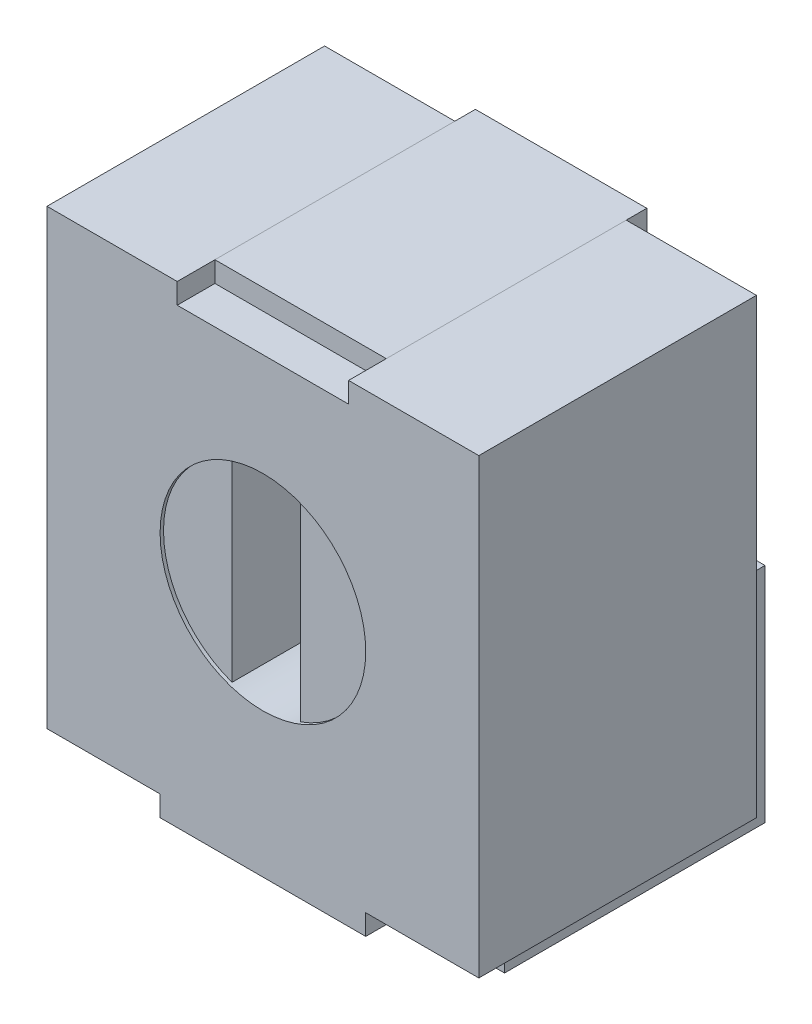
SolidWorks part; units mm, degrees
ref_plane "Front Plane" through (0, 0, 0) normal (0, 0, 1) x (1, 0, 0)
ref_plane "Top Plane" through (0, 0, 0) normal (0, 1, 0) x (1, 0, 0)
ref_plane "Right Plane" through (0, 0, 0) normal (1, 0, 0) x (0, 0, -1)
sketch "Sketch1" plane through (0, 0, 0) normal (0, 0, 1) x (1, 0, 0)
  line L0 (1.6002, 3.2004) -> (1.6002, -0.1524) construction
  line L1 (0, 0) -> (0.8382, 0)
  line L2 (0, 0) -> (0, 3.3528)
  line L3 (0, 3.3528) -> (0.9652, 3.3528)
  line L4 (3.2004, 0) -> (3.2004, 3.3528)
  line L5 (2.3622, 0) -> (3.2004, 0)
  line L6 (2.2352, 3.3528) -> (3.2004, 3.3528)
  line L7 (0.8382, 0) -> (0.8382, -0.1524)
  line L8 (0.8382, -0.1524) -> (2.3622, -0.1524)
  line L9 (2.3622, 0) -> (2.3622, -0.1524)
  line L10 (0, 1.6764) -> (3.2004, 1.6764) construction
  line L11 (0.9652, 3.3528) -> (0.9652, 3.2004)
  line L12 (0.9652, 3.2004) -> (2.2352, 3.2004)
  line L13 (2.2352, 3.3528) -> (2.2352, 3.2004)
  point P5 (1.6002, 3.2004)
  point P18 (1.6002, 1.6764)
  point P20 (1.6002, -0.1524)
  dimension "D1" = 3.2004
  dimension "D2" = 3.3528
  dimension "D3" = 1.524
  dimension "D4" = 0.1524
  dimension "D5" = 1.27
  dimension "D6" = 0.1524
extrude "Boss-Extrude1" add sketch "Sketch1" along normal blind 2.0574
sketch "Sketch2" plane through (0, 0, 2.0574) normal (0, 0, 1) x (1, 0, 0)
  line L0 (0, 1.6764) -> (3.2004, 1.6764) construction
  line L1 (0, 3.3528) -> (0, 0) construction
  line L2 (3.2004, 0) -> (3.2004, 3.3528) construction
  circle A0 centre (1.6002, 1.6764) radius 0.762
  dimension "D1" = 1.524
extrude "Cut-Extrude1" cut sketch "Sketch2" against normal blind 0.0254
sketch "Sketch3" plane through (0, 0, 2.032) normal (0, 0, 1) x (1, 0, 0)
  line L0 (1.6002, 2.4384) -> (1.6002, 0.9144) construction
  line L1 (1.3462, 2.3948) -> (1.3462, 0.958)
  line L2 (1.8542, 2.3948) -> (1.8542, 0.958)
  line L3 (1.3462, 1.6764) -> (1.8542, 1.6764) construction
  circle A0 centre (1.6002, 1.6764) radius 0.762 construction
  circle A1 centre (1.6002, 1.6764) radius 0.762 construction
  arc A2 (1.3462, 2.3948) -> (1.8542, 2.3948) centre (1.6002, 1.6764) cw
  arc A3 (1.3462, 0.958) -> (1.8542, 0.958) centre (1.6002, 1.6764) ccw
  point P13 (1.6002, 1.6764)
  dimension "D2" = 0.762
  dimension "D3" = 0.762
  dimension "D1" = 0.508
extrude "Cut-Extrude2" cut sketch "Sketch3" against normal blind 0.508
ref_plane "Plane1" through (1.6002, 0, 0) normal (-1, 0, 0) x (0, 0, 1)
ref_plane "Plane2" through (0.4191, 0, 0) normal (-1, 0, 0) x (0, 0, 1)
sketch "Sketch5" plane through (1.6002, 0, 0) normal (-1, 0, 0) x (0, 0, 1)
  line L0 (1.778, 3.2004) -> (0, 3.2004)
  line L1 (0, 3.2004) -> (0, 1.6764)
  line L3 (0, 3.3528) -> (0, 0) construction
  line L4 (2.0574, 3.3528) -> (0, 3.3528) construction
  dimension "D1" = 0.1524
  dimension "D2" = 0
  dimension "D3" = 1.778
  dimension "D4" = 1.524
extrude "Extrude-Thin1" add sketch "Sketch5" along normal mid plane 1.27 separate body thin
sketch "Sketch8" plane through (0.4191, 0, 0) normal (-1, 0, 0) x (0, 0, 1)
  line L0 (1.778, 0) -> (0, 0)
  line L1 (2.0574, 0) -> (0, 0) construction
  line L2 (0, 0) -> (0, 1.4986)
  line L3 (0, 3.3528) -> (0, 0) construction
  dimension "D1" = 1.778
  dimension "D2" = 1.4986
extrude "Extrude-Thin6" add sketch "Sketch8" along normal mid plane 0.6604 thin thin type one direction reverse wall 0.1524
chamfer "Chamfer1" distance 0.381 angle 55 1 edges at (0.7493, 1.4986, -0.0762)
mirror "Mirror1" about plane through (1.6002, 0, 0) normal (-1, 0, 0) of "Chamfer1", "Extrude-Thin6"
